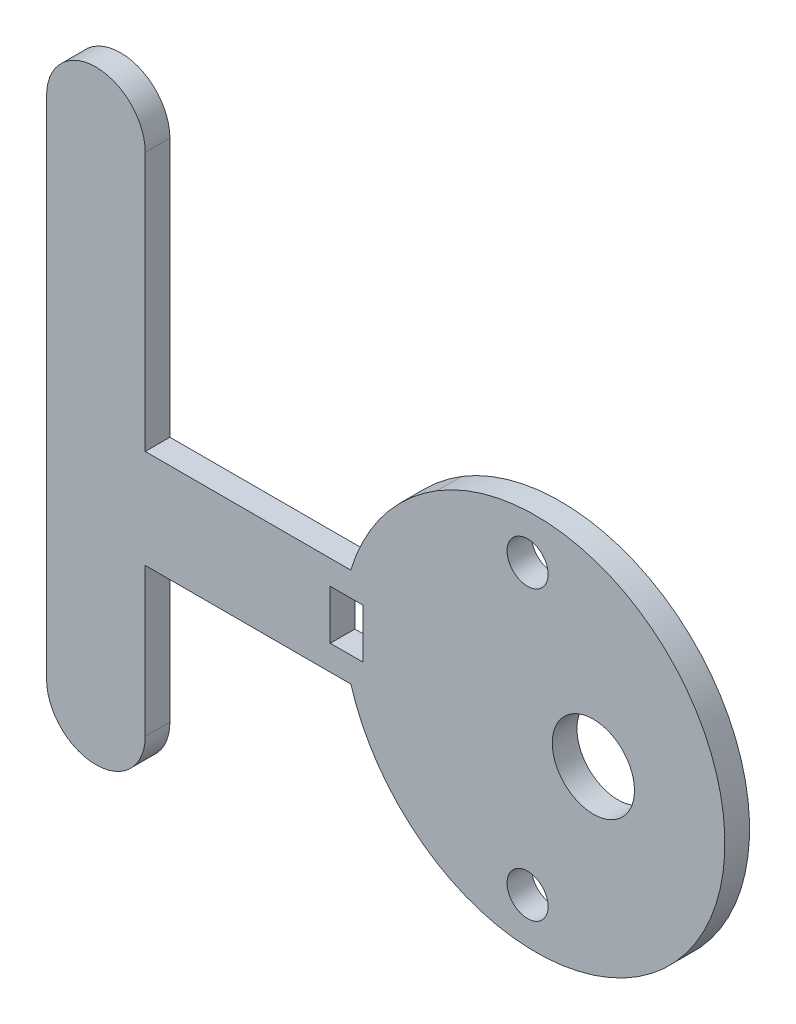
SolidWorks part; units mm, degrees
ref_plane "前视基准面" through (0, 0, 0) normal (0, 0, 1) x (1, 0, 0)
ref_plane "上视基准面" through (0, 0, 0) normal (0, 1, 0) x (1, 0, 0)
ref_plane "右视基准面" through (0, 0, 0) normal (1, 0, 0) x (0, 0, -1)
sketch "草图1" plane through (0, 0, 0) normal (0, 0, 1) x (1, 0, 0)
  line L0 (129.2042, 57.9994) -> (129.2097, 45.9994) construction
  line L10 (129.2097, 51.9994) -> (99.2042, 51.9994) construction
  line L13 (129.2042, 57.9994) -> (104.2042, 57.9994) construction
  line L14 (104.2042, 89.4994) -> (104.2042, 57.9994)
  line L15 (129.2042, 57.9994) -> (104.2042, 57.9994)
  line L16 (129.2097, 45.9994) -> (104.2042, 45.9994)
  line L19 (104.2042, 27.9994) -> (104.2042, 45.9994)
  line L20 (92.2042, 89.4994) -> (92.2042, 27.9994)
  arc A0 (104.2042, 89.4994) -> (92.2042, 89.4994) centre (98.2042, 89.4994) ccw
  circle A1 centre (158.7042, 52.0489) radius 5
  circle A2 centre (150.7042, 69.5489) radius 2.5
  circle A3 centre (150.7042, 34.5489) radius 2.5
  arc A4 (139.601, 32.4415) -> (139.69, 71.6121) centre (151.7042, 51.9994) ccw
  arc A5 (92.2042, 27.9994) -> (104.2042, 27.9994) centre (98.2042, 27.9994) ccw
  arc A8 (139.69, 71.6121) -> (129.2042, 57.9994) centre (152.2687, 51.0779) ccw
  arc A9 (139.601, 32.4415) -> (129.2097, 45.9994) centre (152.2686, 52.9116) cw
  point P0 (98.2042, 51.9994)
  point P21 (99.2042, 51.9994)
  point P23 (113.2042, 51.9994)
  point P24 (50, 20)
extrude "凸台-拉伸1" add sketch "草图1" along normal blind 3
sketch "草图2" plane through (0, 0, 3) normal (0, 0, 1) x (1, 0, 0)
  line L0 (128.7042, 52.0489) -> (153.7042, 52.0489) construction
  line L2 (126.7042, 55.0489) -> (130.7042, 55.0489)
  line L3 (126.7042, 55.0489) -> (126.7042, 49.0489)
  line L4 (126.7042, 49.0489) -> (130.7042, 49.0489)
  line L5 (130.7042, 55.0489) -> (130.7042, 49.0489)
  line L6 (126.7042, 55.0489) -> (130.7042, 49.0489) construction
  line L7 (126.7042, 49.0489) -> (130.7042, 55.0489) construction
  circle A0 centre (158.7042, 52.0489) radius 5 construction
extrude "切除-拉伸1" cut sketch "草图2" against normal blind 3
